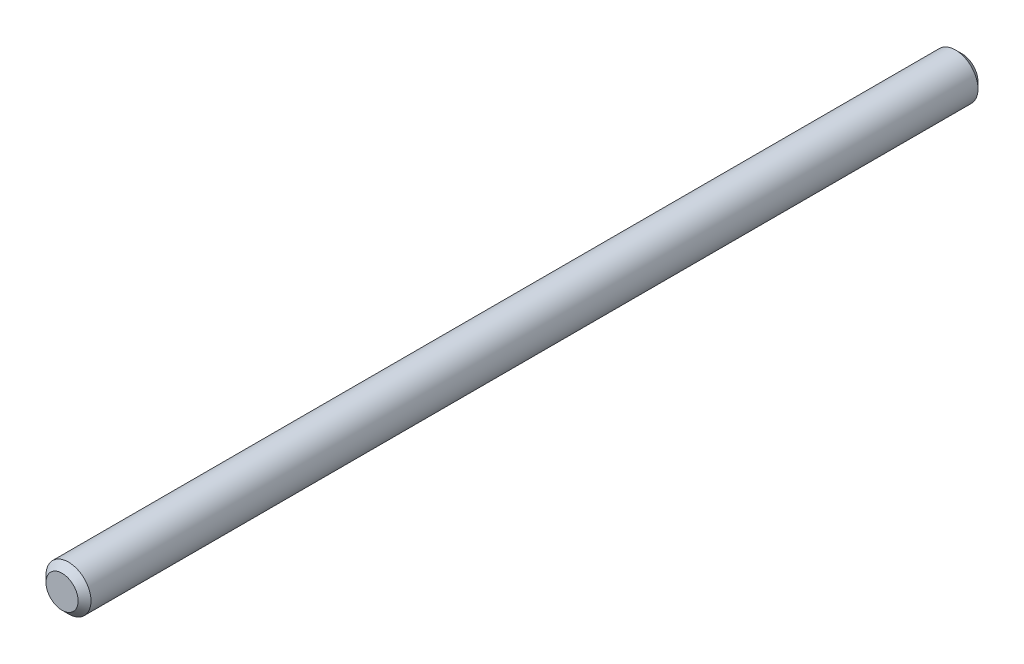
SolidWorks part; units mm, degrees
ref_plane "Front Plane" through (0, 0, 0) normal (0, 0, 1) x (1, 0, 0)
ref_plane "Top Plane" through (0, 0, 0) normal (0, 1, 0) x (1, 0, 0)
ref_plane "Right Plane" through (0, 0, 0) normal (1, 0, 0) x (0, 0, -1)
sketch "Sketch1" plane through (0, 0, 0) normal (0, 0, 1) x (1, 0, 0)
  circle A0 centre (0, 0) radius 1.75
  dimension "D1" = 3.5
extrude "Boss-Extrude1" add sketch "Sketch1" along normal blind 70
chamfer "Chamfer1" distance 0.5 angle 45 2 edges at (1.75, 0, 0) (1.75, 0, 70)
